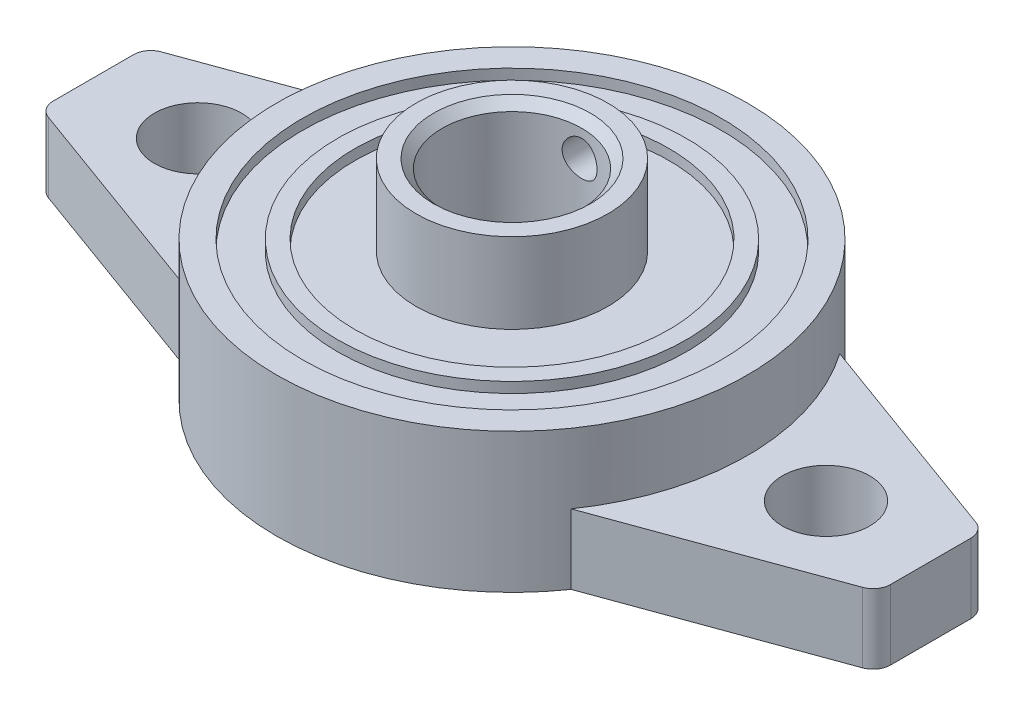
SolidWorks part; units mm, degrees
ref_plane "前视基准面" through (0, 0, 0) normal (0, 0, 1) x (1, 0, 0)
ref_plane "上视基准面" through (0, 0, 0) normal (0, 1, 0) x (1, 0, 0)
ref_plane "右视基准面" through (0, 0, 0) normal (1, 0, 0) x (0, 0, -1)
sketch "草图1" plane through (0, 0, 0) normal (0, 1, 0) x (1, 0, 0)
  line L0 (0, 0) -> (0, 15.5042) construction
  line L1 (-18, 0) -> (18, 0) construction
  line L2 (0, 0) -> (24, 0) construction
  line L3 (24, -2.2998) -> (24, 2.2998)
  line L4 (23.342, 3.2395) -> (11.0894, 7.6991)
  line L5 (23.342, -3.2395) -> (11.0894, -7.6991)
  line L6 (-23.342, 3.2395) -> (-11.0894, 7.6991)
  line L7 (-24, -2.2998) -> (-24, 2.2998)
  line L8 (-23.342, -3.2395) -> (-11.0894, -7.6991)
  circle A0 centre (-18, 0) radius 2.5
  circle A1 centre (18, 0) radius 2.5
  arc A2 (-11.0894, -7.6991) -> (11.0894, -7.6991) centre (0, 0) ccw
  arc A3 (11.0894, 7.6991) -> (-11.0894, 7.6991) centre (0, 0) ccw
  arc A4 (23.342, -3.2395) -> (24, -2.2998) centre (23, -2.2998) ccw
  arc A5 (24, 2.2998) -> (23.342, 3.2395) centre (23, 2.2998) ccw
  arc A6 (-24, -2.2998) -> (-23.342, -3.2395) centre (-23, -2.2998) ccw
  arc A7 (-23.342, 3.2395) -> (-24, 2.2998) centre (-23, 2.2998) ccw
  point P18 (24, -3)
  point P21 (24, 3)
  point P24 (-24, -3)
  point P27 (-24, 3)
  dimension "D2" = 5
  dimension "D3" = 5
  dimension "D4" = 27
  dimension "D8" = 1
  dimension "D1" = 36
  dimension "D5" = 24
  dimension "D6" = 3
  dimension "D7" = 110
extrude "凸台-拉伸1" add sketch "草图1" along normal blind 4
sketch "草图2" plane through (0, 4, 0) normal (0, 1, 0) x (1, 0, 0)
  circle A0 centre (0, 0) radius 13.5
extrude "凸台-拉伸2" add sketch "草图2" along normal blind 4
sketch "草图3" plane through (0, 8, 0) normal (0, 1, 0) x (1, 0, 0)
  circle A0 centre (0, 0) radius 5.5
  dimension "D1" = 11
extrude "凸台-拉伸3" add sketch "草图3" along normal blind 4
sketch "草图4" plane through (0, 12, 0) normal (0, 1, 0) x (1, 0, 0)
  circle A0 centre (0, 0) radius 4
  dimension "D1" = 8
extrude "切除-拉伸1" cut sketch "草图4" against normal through all
sketch "草图5" plane through (0, 8, 0) normal (0, 1, 0) x (1, 0, 0)
  circle A0 centre (0, 0) radius 12
  circle A1 centre (0, 0) radius 10
  circle A2 centre (0, 0) radius 9
  circle M2 centre (0, 0) radius 5.5
  dimension "D1" = 24
  dimension "D2" = 20
  dimension "D3" = 18
extrude "切除-拉伸2" cut sketch "草图5" against normal blind 0.6 contours A0 A1 | A2 M2
sketch "草图8" plane through (0, 0, 0) normal (0, -1, 0) x (1, 0, 0)
  circle A1 centre (0, 0) radius 12.5
  arc A2 (10.2679, 7.1288) -> (-10.2679, 7.1288) centre (0, 0) ccw
  arc A3 (10.2679, 7.1288) -> (-10.2679, 7.1288) centre (0, 0) ccw
  dimension "D1" = 1
extrude "切除-拉伸4" cut sketch "草图8" against normal blind 1 contours A1
sketch "草图9" plane through (0, 0, 0) normal (0, 0, 1) x (1, 0, 0)
  line L0 (0, 12) -> (0, 10) construction
  line L1 (5.5, 12) -> (-5.5, 12) construction
  line L2 (4, 12) -> (-4, 12) construction
  circle A0 centre (0, 10) radius 1
  dimension "D1" = 2
  dimension "D2" = 2
extrude "切除-拉伸5" cut sketch "草图9" against normal through all
chamfer "倒角1" distance 0.5 angle 45 2 edges at (0, 1, -4) (0, 12, 4)
